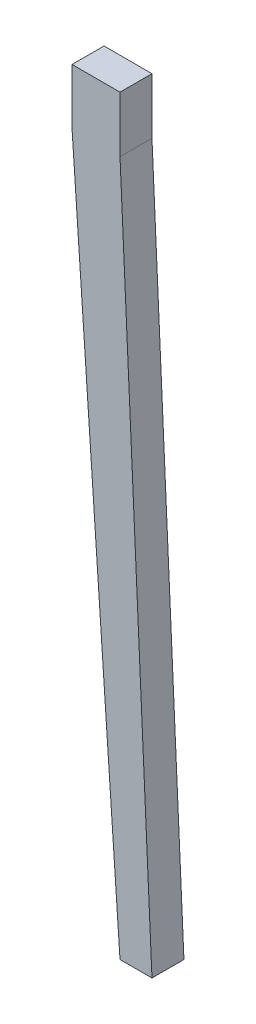
SolidWorks part; units mm, degrees
ref_plane "Front Plane" through (0, 0, 0) normal (0, 0, 1) x (1, 0, 0)
ref_plane "Top Plane" through (0, 0, 0) normal (0, 1, 0) x (1, 0, 0)
ref_plane "Right Plane" through (0, 0, 0) normal (1, 0, 0) x (0, 0, -1)
sketch "Sketch1" plane through (0, 0, 0) normal (0, 0, 1) x (1, 0, 0)
  line L0 (19.05, 0) -> (19.05, 50000) construction
  line L1 (0, 0) -> (38.1, 0)
  line L2 (0, 0) -> (0, -44.45)
  line L3 (0, -44.45) -> (38.1, -44.45)
  line L4 (38.1, 0) -> (38.1, -44.45)
  line L5 (63.5, -1374.6457) -> (63.5, 48625.3543) construction
  line L6 (38.1, -44.45) -> (63.5, -596.9)
  line L7 (-949.1892, -596.9) -> (49050.8108, -596.9) construction
  line L8 (63.5, -596.9) -> (38.1, -596.9)
  line L9 (38.1, -596.9) -> (0, -44.45)
  point P8 (19.05, 0)
  dimension "D1" = 44.45
  dimension "D2" = 38.1
  dimension "D3" = 596.9
  dimension "D4" = 44.45
extrude "Boss-Extrude1" add sketch "Sketch1" along normal blind 25.4 contours L4 L1 L2 L3 | L9 L8 L6 L3
